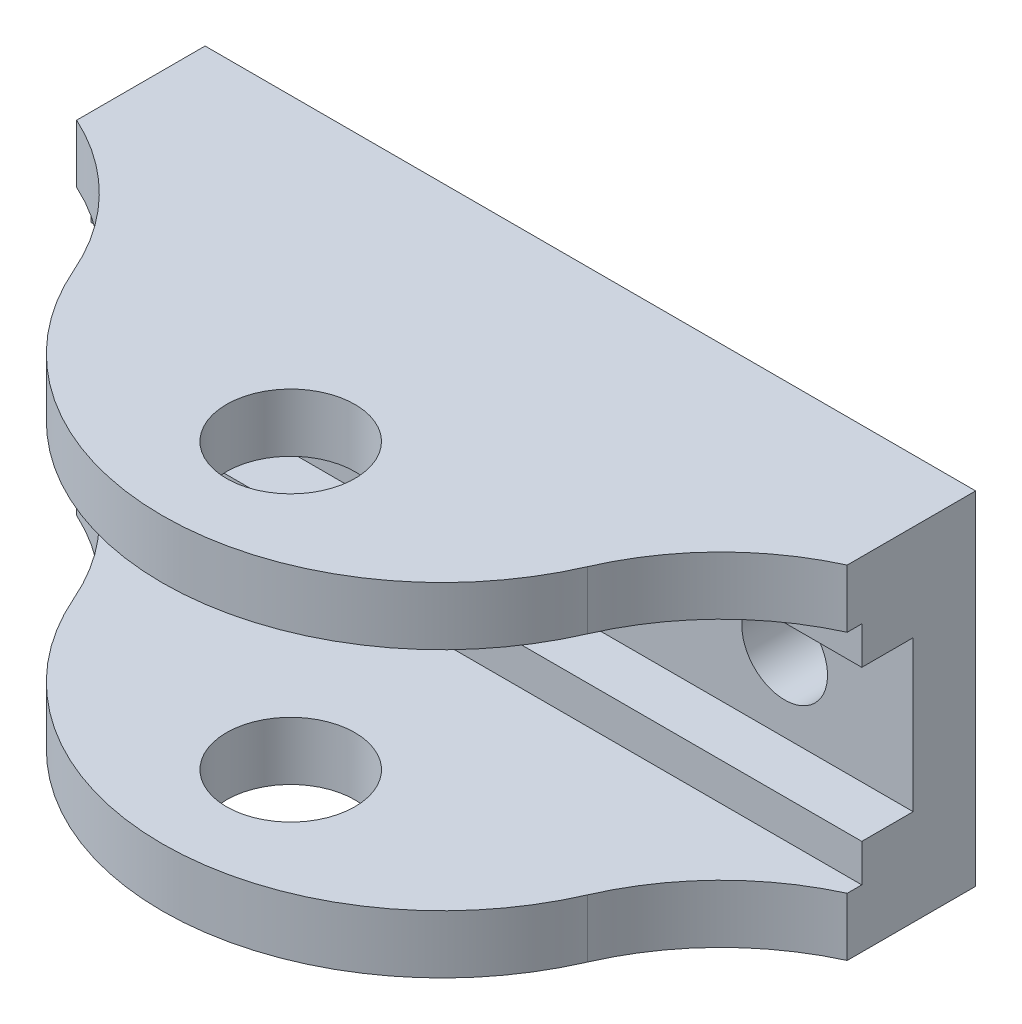
SolidWorks part; units mm, degrees
material "6061-T6 (SS)"
ref_plane "Front Plane" through (0, 0, 0) normal (0, 0, 1) x (1, 0, 0)
ref_plane "Top Plane" through (0, 0, 0) normal (0, 1, 0) x (1, 0, 0)
ref_plane "Right Plane" through (0, 0, 0) normal (1, 0, 0) x (0, 0, -1)
sketch "Sketch2" plane through (0, 0, 0) normal (0, 0, 1) x (1, 0, 0)
  line L0 (-22.225, 0) -> (22.225, 0) construction
  line L1 (-22.225, 12.7) -> (22.225, 12.7) construction
  line L2 (-22.225, -12.7) -> (22.225, -12.7) construction
  line L3 (-19.05, 0) -> (0, 12.7) construction
  line L4 (0, 12.7) -> (19.05, 0) construction
  line L5 (-22.225, 12.7) -> (-28.575, 12.7)
  line L6 (-28.575, 12.7) -> (-28.575, -12.7)
  line L7 (-28.575, -12.7) -> (-22.225, -12.7)
  line L8 (0, 12.7) -> (0, -12.7) construction
  line L9 (28.575, -12.7) -> (22.225, -12.7)
  line L10 (28.575, 12.7) -> (28.575, -12.7)
  line L11 (22.225, 12.7) -> (28.575, 12.7)
  line L12 (-22.225, 12.7) -> (22.225, 12.7)
  line L13 (22.225, -12.7) -> (-22.225, -12.7)
  arc A0 (-22.225, 12.7) -> (-22.225, -12.7) centre (-22.225, 0) ccw construction
  arc A1 (22.225, -12.7) -> (22.225, 12.7) centre (22.225, 0) ccw construction
  circle A2 centre (19.05, 0) radius 3.175
  circle A3 centre (-19.05, 0) radius 3.175
  point P3 (0, 0)
  dimension "D4" = 6.35
  dimension "D1" = 25.4
  dimension "D2" = 44.45
  dimension "D3" = 38.1
  dimension "D5" = 57.15
extrude "Extrude1" add sketch "Sketch2" along normal blind 38.1
sketch "Sketch3" plane through (0, 0, 38.1) normal (0, 0, 1) x (1, 0, 0)
  line L0 (-28.575, 12.7) -> (-28.575, -12.7) construction
  line L1 (-28.575, 5.588) -> (28.575, 5.588)
  line L2 (-28.575, 5.588) -> (-28.575, -5.588)
  line L3 (-28.575, -5.588) -> (28.575, -5.588)
  line L4 (28.575, 5.588) -> (28.575, -5.588)
  line L5 (28.575, -12.7) -> (28.575, 12.7) construction
  line L6 (0, 5.588) -> (0, -5.588) construction
  dimension "D1" = 11.176
extrude "Extrude2" cut sketch "Sketch3" against normal offset from surface (33.4645 mm away) 4.6355 up to face at (22.225, 0, 0)
sketch "Sketch4" plane through (0, 0, 38.1) normal (0, 0, 1) x (1, 0, 0)
  line L1 (-28.575, 12.7) -> (-28.575, 5.588) construction
  line L2 (-28.575, 8.382) -> (28.575, 8.382)
  line L3 (-28.575, 8.382) -> (-28.575, -8.382)
  line L4 (-28.575, -8.382) -> (28.575, -8.382)
  line L5 (28.575, 8.382) -> (28.575, -8.382)
  line L6 (28.575, -12.7) -> (28.575, -5.588) construction
  line L7 (0, 8.382) -> (0, -8.382) construction
  dimension "D1" = 16.764
extrude "Extrude3" cut sketch "Sketch4" against normal offset from surface (29.6545 mm away) 3.81 up to face at (15.875, 0, 4.6355)
sketch "Sketch5" plane through (0, 12.7, 0) normal (0, 1, 0) x (-1, 0, 0)
  line L1 (-28.575, 0) -> (28.575, 0) construction
  circle A0 centre (0, 22.225) radius 4.7625
  dimension "D1" = 9.525
  dimension "D2" = 22.225
extrude "Extrude4" cut sketch "Sketch5" against normal through all
sketch "Sketch6" plane through (0, 12.7, 0) normal (0, 1, 0) x (1, 0, 0)
  line L0 (28.575, -38.1) -> (-28.575, -38.1) construction
  line L1 (28.575, -38.1) -> (28.575, 0) construction
  line L2 (28.575, 0) -> (-28.575, 0) construction
  line L4 (-28.575, -38.1) -> (28.575, -38.1)
  line L5 (0, 0) -> (0, -10.9828) construction
  line L6 (-28.575, -38.1) -> (-28.575, 0) construction
  line L7 (28.575, -38.1) -> (28.575, -9.525)
  line L8 (-28.575, -38.1) -> (-28.575, -9.525)
  arc A0 (28.575, -9.525) -> (19.05, -19.2517) centre (36.5248, -26.837) ccw
  arc A1 (-28.575, -9.525) -> (-19.05, -19.2517) centre (-36.5248, -26.837) cw
  circle A2 centre (0, -22.225) radius 4.7625 construction
  arc A3 (-19.05, -19.2517) -> (19.05, -19.2517) centre (0, -10.9828) ccw
  point P0 (0, -31.75)
  point P16 (0, -22.225)
  dimension "D2" = 9.525
  dimension "D1" = 19.05
  dimension "D3" = 9.525
  dimension "D4" = 38.1
extrude "Extrude5" cut sketch "Sketch6" against normal through all
sketch3d "3DSketch2"
  line L0 (0, 12.7, 22.225) -> (0, -12.7, 22.225) construction
  line L1 (0, 8.382, 22.225) -> (0, 12.7, 22.225) construction
  line L2 (0, 8.382, 22.225) -> (0, 12.7, 22.225) construction
  point P6 (0, 0, 22.225)
